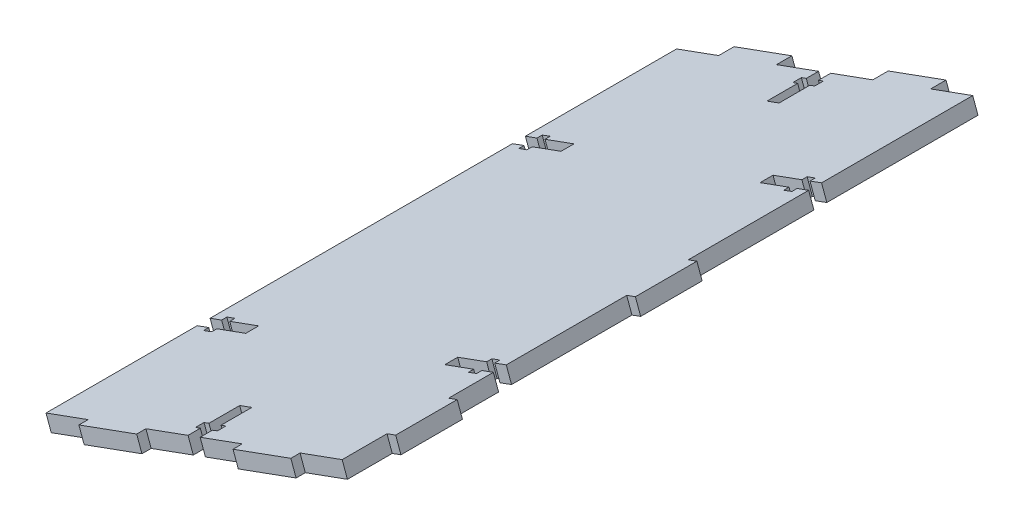
SolidWorks part; units mm, degrees
ref_plane "Front Plane" through (0, 0, 0) normal (0, 0, 1) x (1, 0, 0)
ref_plane "Top Plane" through (0, 0, 0) normal (0, 1, 0) x (1, 0, 0)
ref_plane "Right Plane" through (0, 0, 0) normal (1, 0, 0) x (0, 0, -1)
sketch "Sketch2" plane through (0, 0, 14.2) normal (0, 0, 1) x (1, 0, 0)
  line L12 (-76.8867, -45.5626) -> (-221.9898, -98.3304) construction
  line L17 (-52.9615, -36.8621) -> (-51.2527, -41.561)
  line L18 (-52.9615, -36.8621) -> (-149.2503, -71.8781)
  line L19 (-51.2527, -41.561) -> (-147.5415, -76.5771)
  line L20 (-149.2503, -71.8781) -> (-147.5415, -76.5771)
  line L24 (-138.5053, -101.4251) -> (-127.2272, -132.438) construction
  dimension "D1" = 5
extrude "Boss-Extrude1" add sketch "Sketch2" along normal up to surface (205 mm away)
sketch "Sketch4" plane through (7.3623, -20.2452, 0) normal (0.3418, -0.9398, 0) x (-0.9398, -0.3418, 0)
  line L0 (111.4996, -14.2) -> (115.6996, -14.2)
  line L1 (111.4996, -14.2) -> (111.4996, -18.2)
  line L2 (115.6996, -14.2) -> (115.6996, -18.2)
  line L3 (109.7996, -18.2) -> (111.4996, -18.2)
  line L4 (109.7996, -18.2) -> (109.7996, -21)
  line L5 (117.3996, -18.2) -> (117.3996, -21)
  line L6 (109.7996, -21) -> (111.4996, -21)
  line L7 (111.4996, -21) -> (111.4996, -31)
  line L8 (115.6996, -21) -> (115.6996, -31)
  line L9 (111.4996, -31) -> (115.6996, -31)
  line L10 (115.6996, -21) -> (117.3996, -21)
  line L11 (115.6996, -18.2) -> (117.3996, -18.2)
  line L14 (62.3706, -67.55) -> (62.3706, -63.35)
  line L25 (62.3706, -14.2) -> (164.8286, -14.2) construction
  line L26 (115.6996, -219.2) -> (111.4996, -219.2)
  line L27 (115.6996, -219.2) -> (115.6996, -215.2)
  line L28 (113.5996, -31) -> (113.5996, -14.2) construction
  line L29 (111.4996, -219.2) -> (111.4996, -215.2)
  line L30 (117.3996, -215.2) -> (115.6996, -215.2)
  line L31 (117.3996, -215.2) -> (117.3996, -212.4)
  line L32 (109.7996, -215.2) -> (109.7996, -212.4)
  line L33 (117.3996, -212.4) -> (115.6996, -212.4)
  line L34 (115.6996, -212.4) -> (115.6996, -202.4)
  line L35 (111.4996, -212.4) -> (111.4996, -202.4)
  line L36 (115.6996, -202.4) -> (111.4996, -202.4)
  line L37 (111.4996, -212.4) -> (109.7996, -212.4)
  line L38 (111.4996, -215.2) -> (109.7996, -215.2)
  line L39 (113.5996, -202.4) -> (113.5996, -219.2) construction
  line L40 (62.3706, -219.2) -> (164.8286, -219.2) construction
  line L41 (62.3706, -67.55) -> (66.3706, -67.55)
  line L42 (62.3706, -63.35) -> (66.3706, -63.35)
  line L43 (66.3706, -69.25) -> (66.3706, -67.55)
  line L44 (66.3706, -69.25) -> (69.1706, -69.25)
  line L45 (66.3706, -61.65) -> (69.1706, -61.65)
  line L46 (69.1706, -69.25) -> (69.1706, -67.55)
  line L47 (69.1706, -67.55) -> (79.1706, -67.55)
  line L48 (69.1706, -63.35) -> (79.1706, -63.35)
  line L49 (79.1706, -67.55) -> (79.1706, -63.35)
  line L50 (69.1706, -63.35) -> (69.1706, -61.65)
  line L51 (66.3706, -63.35) -> (66.3706, -61.65)
  line L52 (79.1706, -65.45) -> (62.3706, -65.45) construction
  line L55 (62.3706, -219.2) -> (62.3706, -14.2) construction
  line L56 (62.3706, -14.2) -> (62.3706, -116.7) construction
  line L57 (62.3706, -116.7) -> (164.8286, -116.7) construction
  line L58 (79.1706, -167.95) -> (62.3706, -167.95) construction
  line L59 (66.3706, -170.05) -> (66.3706, -171.75)
  line L60 (69.1706, -170.05) -> (69.1706, -171.75)
  line L61 (79.1706, -165.85) -> (79.1706, -170.05)
  line L62 (69.1706, -170.05) -> (79.1706, -170.05)
  line L63 (69.1706, -165.85) -> (79.1706, -165.85)
  line L64 (69.1706, -164.15) -> (69.1706, -165.85)
  line L65 (66.3706, -171.75) -> (69.1706, -171.75)
  line L66 (66.3706, -164.15) -> (69.1706, -164.15)
  line L67 (66.3706, -164.15) -> (66.3706, -165.85)
  line L68 (62.3706, -170.05) -> (66.3706, -170.05)
  line L69 (62.3706, -165.85) -> (66.3706, -165.85)
  line L70 (62.3706, -165.85) -> (62.3706, -170.05)
  line L76 (164.8286, -219.2) -> (164.8286, -14.2) construction
  line L77 (113.5996, -171.4513) -> (113.5996, -40.1199) construction
  line L78 (148.0286, -167.95) -> (164.8286, -167.95) construction
  line L87 (164.8286, -14.2) -> (164.8286, -116.7) construction
  line L88 (148.0286, -65.45) -> (164.8286, -65.45) construction
  line L89 (164.8286, -165.85) -> (164.8286, -170.05)
  line L90 (164.8286, -165.85) -> (160.8286, -165.85)
  line L91 (164.8286, -170.05) -> (160.8286, -170.05)
  line L92 (160.8286, -164.15) -> (160.8286, -165.85)
  line L93 (160.8286, -164.15) -> (158.0286, -164.15)
  line L94 (160.8286, -171.75) -> (158.0286, -171.75)
  line L95 (158.0286, -164.15) -> (158.0286, -165.85)
  line L96 (158.0286, -165.85) -> (148.0286, -165.85)
  line L97 (158.0286, -170.05) -> (148.0286, -170.05)
  line L98 (148.0286, -165.85) -> (148.0286, -170.05)
  line L99 (158.0286, -170.05) -> (158.0286, -171.75)
  line L100 (160.8286, -170.05) -> (160.8286, -171.75)
  line L101 (160.8286, -63.35) -> (160.8286, -61.65)
  line L102 (158.0286, -63.35) -> (158.0286, -61.65)
  line L103 (148.0286, -67.55) -> (148.0286, -63.35)
  line L104 (158.0286, -63.35) -> (148.0286, -63.35)
  line L105 (158.0286, -67.55) -> (148.0286, -67.55)
  line L106 (158.0286, -69.25) -> (158.0286, -67.55)
  line L107 (160.8286, -61.65) -> (158.0286, -61.65)
  line L108 (160.8286, -69.25) -> (158.0286, -69.25)
  line L109 (160.8286, -69.25) -> (160.8286, -67.55)
  line L110 (164.8286, -63.35) -> (160.8286, -63.35)
  line L111 (164.8286, -67.55) -> (160.8286, -67.55)
  line L112 (164.8286, -67.55) -> (164.8286, -63.35)
  point P70 (113.5996, -116.7)
  dimension "D1" = 4.2
  dimension "D2" = 1.7
  dimension "D3" = 1.7
  dimension "D4" = 2.8
  dimension "D5" = 10
  dimension "D6" = 4
  dimension "D7" = 4.2
  dimension "D8" = 1.7
  dimension "D9" = 1.7
  dimension "D10" = 2.8
  dimension "D11" = 10
  dimension "D12" = 4
  dimension "D13" = 4.2
  dimension "D14" = 1.7
  dimension "D15" = 1.7
  dimension "D16" = 2.8
  dimension "D17" = 10
  dimension "D18" = 4
extrude "Cut-Extrude3" cut sketch "Sketch4" against normal through all
sketch "Sketch5" plane through (7.3623, -20.2452, 0) normal (0.3418, -0.9398, 0) x (0.9398, 0.3418, 0)
  line L0 (-130.2641, 219.2) -> (-150.2641, 219.2)
  line L1 (-130.2641, 219.2) -> (-130.2641, 222.2)
  line L2 (-150.2641, 219.2) -> (-150.2641, 222.2)
  line L3 (-130.2641, 222.2) -> (-150.2641, 222.2)
  line L4 (-164.8286, 219.2) -> (-115.6996, 219.2) construction
  line L5 (-76.9351, 219.2) -> (-96.9351, 219.2)
  line L6 (-76.9351, 219.2) -> (-76.9351, 222.2)
  line L7 (-96.9351, 219.2) -> (-96.9351, 222.2)
  line L8 (-76.9351, 222.2) -> (-96.9351, 222.2)
  line L9 (-111.4996, 219.2) -> (-62.3706, 219.2) construction
  line L10 (-62.3706, 106.7) -> (-62.3706, 126.7)
  line L11 (-62.3706, 106.7) -> (-59.3706, 106.7)
  line L12 (-62.3706, 126.7) -> (-59.3706, 126.7)
  line L13 (-59.3706, 106.7) -> (-59.3706, 126.7)
  line L14 (-62.3706, 67.55) -> (-62.3706, 165.85) construction
  line L15 (-62.3706, 204.625) -> (-62.3706, 184.625)
  line L16 (-62.3706, 204.625) -> (-59.3706, 204.625)
  line L17 (-62.3706, 184.625) -> (-59.3706, 184.625)
  line L18 (-59.3706, 204.625) -> (-59.3706, 184.625)
  line L19 (-62.3706, 170.05) -> (-62.3706, 219.2) construction
  line L20 (-62.3706, 92.4) -> (-62.3706, 141)
  line L24 (-62.3706, 67.55) -> (-62.3706, 165.85) construction
  line L25 (-150.2641, 14.2) -> (-130.2641, 14.2)
  line L26 (-150.2641, 14.2) -> (-150.2641, 9.2)
  line L27 (-130.2641, 14.2) -> (-130.2641, 9.2)
  line L28 (-150.2641, 9.2) -> (-130.2641, 9.2)
  line L29 (-164.8286, 14.2) -> (-115.6996, 14.2) construction
  line L30 (-96.9351, 14.2) -> (-76.9351, 14.2)
  line L31 (-96.9351, 14.2) -> (-96.9351, 9.2)
  line L32 (-76.9351, 14.2) -> (-76.9351, 9.2)
  line L33 (-96.9351, 9.2) -> (-76.9351, 9.2)
  line L34 (-111.4996, 14.2) -> (-62.3706, 14.2) construction
  line L35 (25.1714, 222.2) -> (-242.2286, 222.2) construction
  point P10 (-140.2641, 219.2)
  point P11 (-86.9351, 219.2)
  point P16 (-62.3706, 116.7)
  point P23 (-62.3706, 194.625)
  point P31 (-62.3706, 116.7)
  point P39 (-140.2641, 14.2)
  point P49 (-86.9351, 14.2)
  dimension "D2" = 20
  dimension "D4" = 20
  dimension "D5" = 3
  dimension "D6" = 20
  dimension "D7" = 3
  dimension "D8" = 20
  dimension "D11" = 5
  dimension "D12" = 20
  dimension "D13" = 5
  dimension "D14" = 20
extrude "Boss-Extrude2" add sketch "Sketch5" against normal blind 5 contours L31 L33 L32 L30 | L26 L28 L27 L25 | L11 L13 L12 L10 | L18 L16 L15 L17 | L6 L8 L7 L5 | L1 L3 L2 L0
